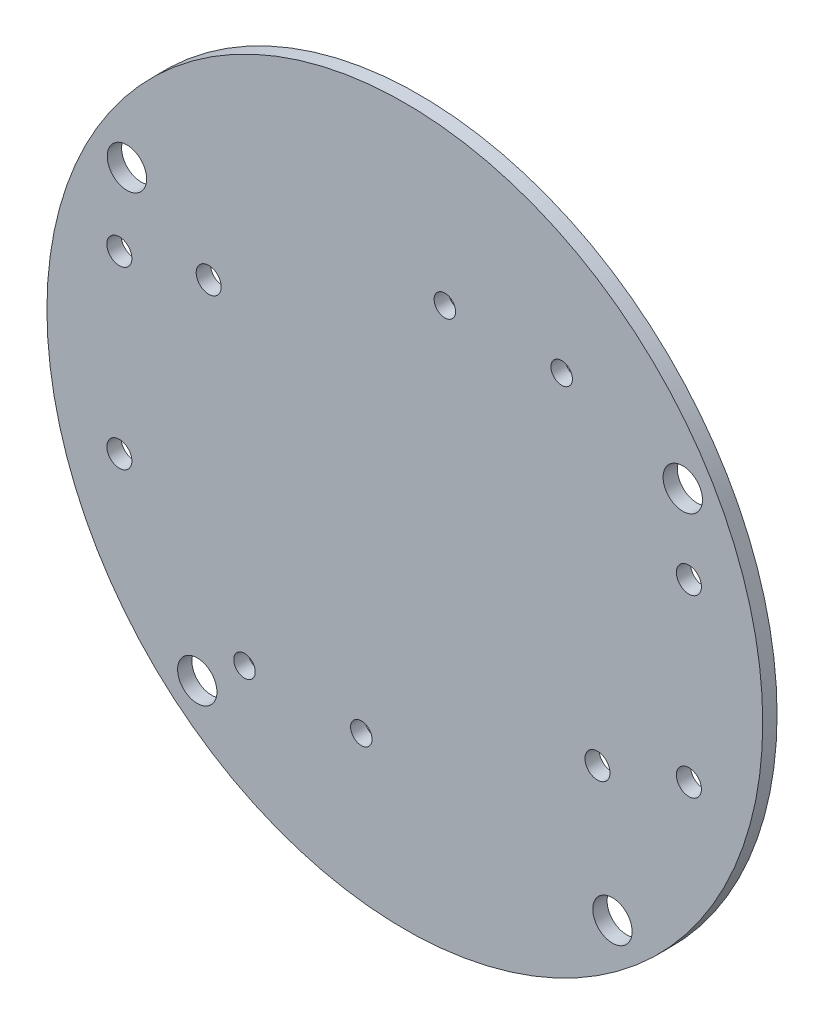
SolidWorks part; units mm, degrees
ref_plane "Plano frontal" through (0, 0, 0) normal (0, 0, 1) x (1, 0, 0)
ref_plane "Plano superior" through (0, 0, 0) normal (0, 1, 0) x (1, 0, 0)
ref_plane "Plano direito" through (0, 0, 0) normal (1, 0, 0) x (0, 0, -1)
sketch "Esboço1" plane through (0, 0, 0) normal (0, 0, 1) x (1, 0, 0)
  circle A0 centre (0, 0) radius 50
  dimension "D1" = 100
extrude "Ressalto-extrusão1" add sketch "Esboço1" along normal blind 2
sketch "Esboço2" plane through (0, 0, 2) normal (0, 0, 1) x (1, 0, 0)
  line L0 (0, 0) -> (0, 68.6386) construction
  line L1 (-61.9657, 0) -> (66.0984, 0) construction
  line L2 (-61.9657, -34.4093) -> (66.0984, -34.4093) construction
  line L3 (-65.4234, 22.88) -> (52.1255, 22.88) construction
  circle A4 centre (-29, -34.4093) radius 2.75
  circle A5 centre (29, -34.4093) radius 2.75
  circle A6 centre (-38.8242, 22.7526) radius 2.75
  circle A7 centre (38.8242, 22.7526) radius 2.75
  point P9 (2.9328, -3.8481)
  dimension "D1" = 58
  dimension "D4" = 45
  dimension "D2" = 45
  dimension "D8" = 5.5
  dimension "D9" = 5.5
  dimension "D10" = 5.5
  dimension "D11" = 5.5
  dimension "D3" = 45
  dimension "D5" = 45
  dimension "D6" = 58
  dimension "D7" = 58
extrude "Corte-extrusão1" cut sketch "Esboço2" against normal blind 2
sketch "Esboço3" plane through (0, 0, 2) normal (0, 0, 1) x (1, 0, 0)
  line L0 (71.0424, 0) -> (-71.0424, 0) construction
  line L1 (0, -53.8288) -> (0, 53.8288) construction
  circle A0 centre (-27.4, 14.89) radius 1.75
  circle A1 centre (26.91, -16.73) radius 1.75
  circle A2 centre (-39.88, -12.4) radius 1.75
  circle A3 centre (-39.88, 12.11) radius 1.75
  circle A4 centre (39.68, 12.16) radius 1.75
  circle A5 centre (39.68, -12.34) radius 1.75
  circle A6 centre (5.59, 28.28) radius 1.5
  circle A7 centre (21.91, 28.28) radius 1.5
  circle A8 centre (-6.08, -29.3) radius 1.5
  circle A9 centre (-22.4, -29.3) radius 1.5
  point P4 (0, 0)
  point P8 (0, 0)
  dimension "D1" = 3.5
  dimension "D6" = 12.11
  dimension "D14" = 28.28
  dimension "D22" = 3
  dimension "D23" = 3
  dimension "D24" = 3
  dimension "D25" = 3
  dimension "D2" = 27.4
  dimension "D3" = 14.89
  dimension "D4" = 26.91
  dimension "D5" = 16.73
  dimension "D7" = 12.4
  dimension "D8" = 39.88
  dimension "D9" = 39.88
  dimension "D10" = 12.34
  dimension "D11" = 12.16
  dimension "D12" = 39.68
  dimension "D13" = 39.68
  dimension "D15" = 28.28
  dimension "D16" = 5.59
  dimension "D17" = 21.91
  dimension "D18" = 29.3
  dimension "D19" = 29.3
  dimension "D20" = 6.08
  dimension "D21" = 22.4
extrude "Corte-extrusão2" cut sketch "Esboço3" against normal blind 10
